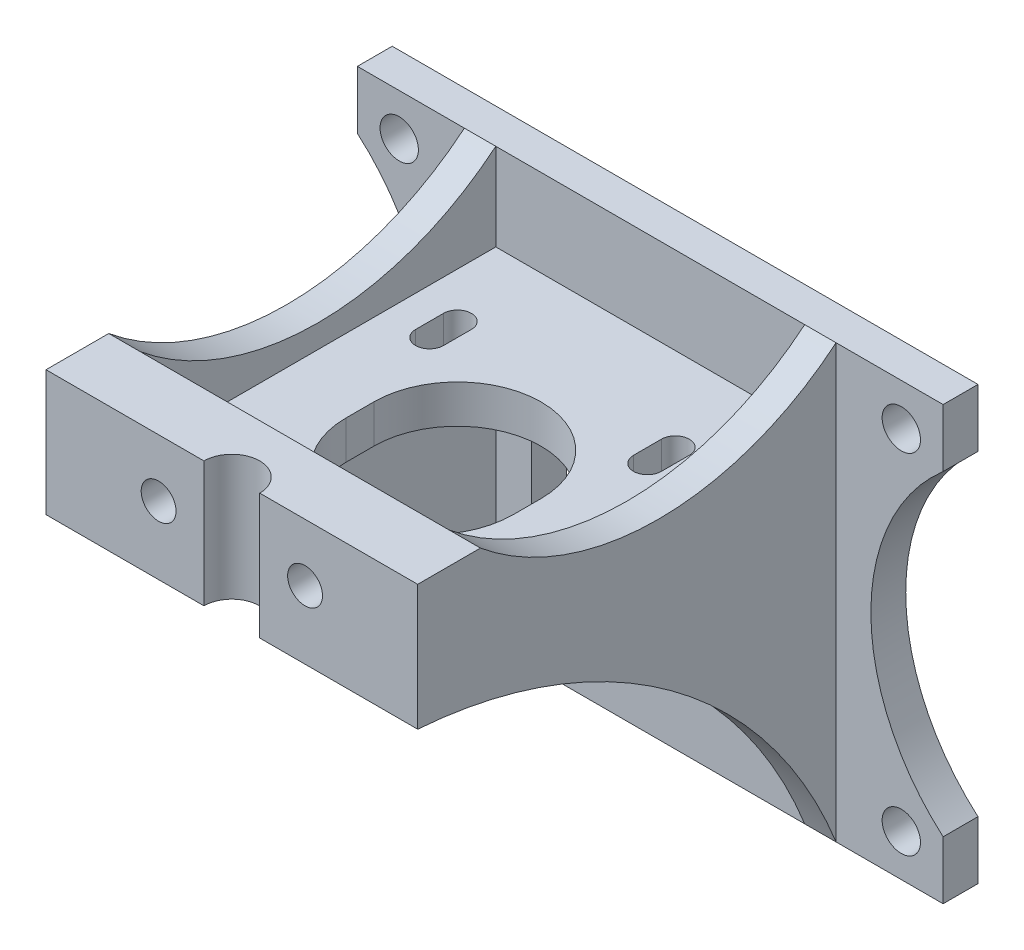
SolidWorks part; units mm, degrees
material "ABS"
ref_plane "Front Plane" through (0, 0, 0) normal (0, 0, 1) x (1, 0, 0)
ref_plane "Top Plane" through (0, 0, 0) normal (0, 1, 0) x (1, 0, 0)
ref_plane "Right Plane" through (0, 0, 0) normal (1, 0, 0) x (0, 0, -1)
sketch "Sketch2" plane through (0, 0, 0) normal (0, 0, 1) x (1, 0, 0)
  line L0 (0, -53.68) -> (0, -62)
  line L1 (0, 0) -> (84, 0)
  line L2 (0, 0) -> (0, -8.32)
  line L3 (0, -62) -> (84, -62)
  line L4 (84, 0) -> (84, -8.32)
  line L5 (25, -20) -> (59, -20)
  line L6 (25, -20) -> (25, -54)
  line L7 (25, -54) -> (59, -54)
  line L8 (59, -20) -> (59, -54)
  line L9 (84, -53.68) -> (84, -62)
  circle A0 centre (6, -6) radius 2.75
  circle A1 centre (78, -56) radius 2.75
  circle A2 centre (6, -56) radius 2.75
  arc A3 (0, -8.32) -> (0, -53.68) centre (-19.6371, -31) cw
  circle A4 centre (78, -6) radius 2.75
  arc A5 (84, -8.32) -> (84, -53.68) centre (103.6371, -31) ccw
  point P24 (0, -8.32)
  point P25 (0, -53.68)
  point P26 (84, -53.68)
  point P27 (84, -8.32)
  dimension "D5" = 6
  dimension "D6" = 5.5
  dimension "D7" = 5.5
  dimension "D8" = 5.5
  dimension "D9" = 6
  dimension "D12" = 6
  dimension "D13" = 6
  dimension "D14" = 6
  dimension "D15" = 6
  dimension "D16" = 6
  dimension "D20" = 30
  dimension "D23" = 30
  dimension "D1" = 62
  dimension "D2" = 84
  dimension "D3" = 34
  dimension "D4" = 34
  dimension "D10" = 6
  dimension "D17" = 20
  dimension "D18" = 8.32
  dimension "D19" = 8.32
  dimension "D21" = 25
  dimension "D22" = 8.32
  dimension "D24" = 8.32
  dimension "D11" = 2
extrude "Boss-Extrude1" add sketch "Sketch2" along normal blind 5
sketch "Sketch3" plane through (0, 0, 5) normal (0, 0, 1) x (1, 0, 0)
  line L0 (84, 0) -> (0, 0) construction
  line L1 (15.35, 0) -> (19.85, 0)
  line L2 (15.35, 0) -> (15.35, -62)
  line L3 (15.35, -62) -> (19.85, -62)
  line L4 (19.85, 0) -> (19.85, -62)
  line L5 (0, -62) -> (84, -62) construction
  line L7 (64.15, 0) -> (68.65, 0)
  line L8 (64.15, 0) -> (64.15, -62)
  line L9 (64.15, -62) -> (68.65, -62)
  line L10 (68.65, 0) -> (68.65, -62)
  line L11 (15.35, 0) -> (68.65, 0)
  line L12 (15.35, 0) -> (15.35, -18)
  line L13 (15.35, -18) -> (68.65, -18)
  line L14 (68.65, 0) -> (68.65, -18)
  line M6 (0, -62) -> (84, -62)
  line M10 (84, 0) -> (0, 0)
  dimension "D1" = 15.35
  dimension "D2" = 4.5
  dimension "D3" = 15.35
  dimension "D4" = 4.5
  dimension "D5" = 18
extrude "Boss-Extrude2" add sketch "Sketch3" along normal blind 60 contours L13 L2 L4 M6 | L13 L8 L10 M6 | L8 L13 L10 M10 | L2 L13 L4 M10 | L4 L13 L8 M10
sketch "Sketch6" plane through (68.65, 0, 0) normal (1, 0, 0) x (0, 0, -1)
  line L0 (-65, 0) -> (-65, -62) construction
  arc A0 (-5, -62) -> (-65, -18) centre (-70.0654, -87.8165) ccw
  dimension "D2" = 70
  dimension "D1" = 18
extrude "Cut-Extrude1" cut sketch "Sketch6" against normal blind 60 and the other way through all
sketch "Sketch7" plane through (68.65, 0, 0) normal (1, 0, 0) x (0, 0, -1)
  line L1 (-65, 0) -> (-5, 0) construction
  arc A0 (-5, 0) -> (-56, 0) centre (-30.5, 30.818) cw
  dimension "D2" = 40
  dimension "D1" = 9
extrude "Cut-Extrude3" cut sketch "Sketch7" against normal blind 60 and the other way through all
sketch "Sketch9" plane through (0, -18, 0) normal (0, -1, 0) x (1, 0, 0)
  line L0 (19.85, 65) -> (64.15, 65) construction
  line L1 (19.85, 56) -> (64.15, 56)
  line L2 (19.85, 56) -> (19.85, 5)
  line L3 (19.85, 5) -> (64.15, 5)
  line L4 (64.15, 56) -> (64.15, 5)
  line L5 (15.35, 65) -> (15.35, 5) construction
  dimension "D1" = 9
  dimension "D2" = 4.5
extrude "Cut-Extrude6" cut sketch "Sketch9" against normal up to next from offset 5.5 offset against normal yes
sketch "Sketch10" plane through (0, -12.5, 0) normal (0, 1, 0) x (1, 0, 0)
  line L0 (26.35, -17) -> (26.35, -21) construction
  line L1 (28.35, -17) -> (28.35, -21)
  line L2 (24.35, -17) -> (24.35, -21)
  line L3 (19.85, -56) -> (19.85, -5) construction
  line L4 (64.15, -5) -> (19.85, -5) construction
  arc A0 (28.35, -17) -> (24.35, -17) centre (26.35, -17) ccw
  arc A1 (24.35, -21) -> (28.35, -21) centre (26.35, -21) ccw
  point P2 (26.35, -19)
  dimension "D3" = 4
  dimension "D4" = 12
  dimension "D1" = 4.5
  dimension "D2" = 4
extrude "Cut-Extrude7" cut sketch "Sketch10" against normal blind 5.5
pattern_linear "LPattern1" count 2 spacing 31.25 along (1, 0, 0) of "Cut-Extrude7"
pattern_linear "LPattern2" count 2 spacing 31 along (0, 0, 1) of "Cut-Extrude7", "LPattern1"
sketch "Sketch11" plane through (0, -12.5, 0) normal (0, 1, 0) x (1, 0, 0)
  line L0 (42.35, -33) -> (42.35, -37) construction
  line L1 (54.35, -33) -> (54.35, -37)
  line L2 (30.35, -33) -> (30.35, -37)
  line L3 (19.85, -56) -> (19.85, -5) construction
  line L4 (64.15, -56) -> (19.85, -56) construction
  arc A0 (54.35, -33) -> (30.35, -33) centre (42.35, -33) ccw
  arc A1 (30.35, -37) -> (54.35, -37) centre (42.35, -37) ccw
  point P2 (42.35, -35)
  dimension "D2" = 4
  dimension "D3" = 10.5
  dimension "D1" = 24
  dimension "D4" = 21
extrude "Cut-Extrude8" cut sketch "Sketch11" against normal blind 10
sketch "Sketch14" plane through (0, -18, 0) normal (0, -1, 0) x (1, 0, 0)
  line L0 (19.85, 65) -> (64.15, 65) construction
  line L1 (42, 97.8927) -> (42, -10.1177) construction
  arc A0 (38, 65) -> (46, 65) centre (42, 65) ccw
  dimension "D2" = 4
  dimension "D1" = 8
extrude "Cut-Extrude10" cut sketch "Sketch14" against normal through all and the other way through all
sketch "Sketch15" plane through (0, 0, 65) normal (0, 0, 1) x (1, 0, 0)
  line L0 (38, -18) -> (38, 0) construction
  line L1 (19.85, -18) -> (38, -18) construction
  circle A0 centre (31.5, -8.25) radius 2.5
  dimension "D1" = 5
  dimension "D2" = 6.5
  dimension "D3" = 9.75
extrude "Cut-Extrude11" cut sketch "Sketch15" against normal blind 4.6
pattern_linear "LPattern3" count 2 spacing 21 along (1, 0, 0) of "Cut-Extrude11"
